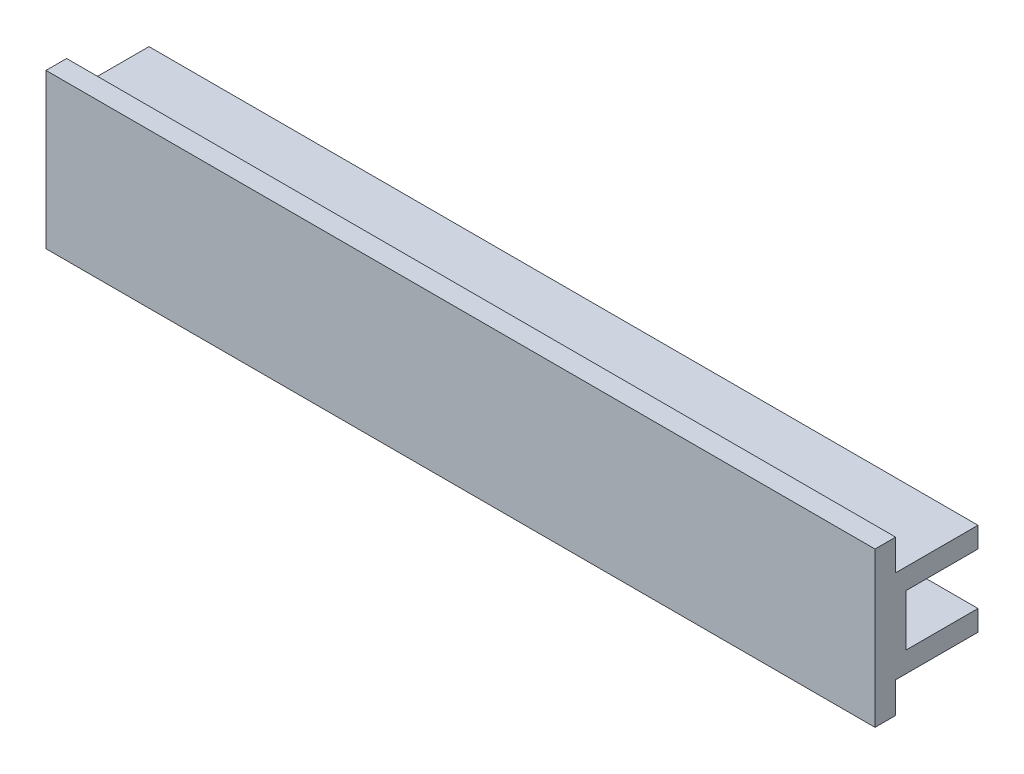
SolidWorks part; units mm, degrees
ref_plane "Front Plane" through (0, 0, 0) normal (0, 0, 1) x (1, 0, 0)
ref_plane "Top Plane" through (0, 0, 0) normal (0, 1, 0) x (1, 0, 0)
ref_plane "Right Plane" through (0, 0, 0) normal (1, 0, 0) x (0, 0, -1)
sketch "Sketch1" plane through (0, 0, 0) normal (1, 0, 0) x (0, 0, -1)
  line L0 (-3, 7.5) -> (-3, 4.5)
  line L1 (-5, 7.5) -> (-3, 7.5)
  line L2 (-5, 7.5) -> (-5, -7.5)
  line L3 (-5, -7.5) -> (-3, -7.5)
  line L4 (5, 4.5) -> (5, 2.5)
  line L5 (-5, 7.5) -> (5, -7.5) construction
  line L6 (-5, -7.5) -> (5, 7.5) construction
  line L7 (-3, 4.5) -> (5, 4.5)
  line L8 (5, 2.5) -> (-2, 2.5)
  line L9 (-2, 2.5) -> (-2, -2.5)
  line L10 (-2, -2.5) -> (5, -2.5)
  line L11 (5, -4.5) -> (-3, -4.5)
  line L12 (-3, -4.5) -> (-3, -7.5)
  line L13 (5, -2.5) -> (5, -4.5)
  point P0 (0, 0)
  dimension "D1" = 15
  dimension "D2" = 10
  dimension "D3" = 2
  dimension "D4" = 2
  dimension "D5" = 2
  dimension "D6" = 5
  dimension "D7" = 3
  dimension "D8" = 7
  dimension "D9" = 10
  dimension "D10" = 5
extrude "Extrude1" add sketch "Sketch1" along normal mid plane 80.5
sketch "Sketch2" plane through (-40.25, 0, 0) normal (-1, 0, 0) x (0, 0, 1)
  line L0 (2, 2.5) -> (3, 2.5)
  line L1 (3, 2.5) -> (3, -2.5)
  line L2 (3, -2.5) -> (2, -2.5)
  line L3 (2, -2.5) -> (2, 2.5)
  dimension "D1" = 1
extrude "Extrude2" cut sketch "Sketch2" against normal blind 22
